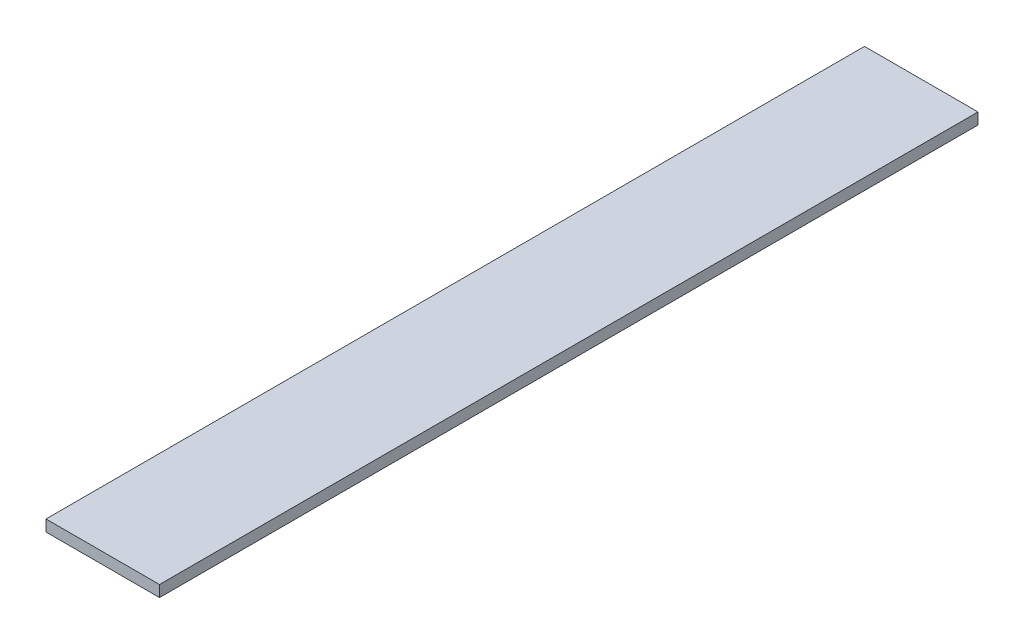
SolidWorks part; units mm, degrees
material "Acrylic (Medium-high impact)"
ref_plane "Front Plane" through (0, 0, 0) normal (0, 0, 1) x (1, 0, 0)
ref_plane "Top Plane" through (0, 0, 0) normal (0, 1, 0) x (1, 0, 0)
ref_plane "Right Plane" through (0, 0, 0) normal (1, 0, 0) x (0, 0, -1)
sketch "Sketch1" plane through (0, 0, 0) normal (0, 0, 1) x (1, 0, 0)
  line L1 (0, 0) -> (47.7, 0)
  line L2 (0, 0) -> (0, 4.7625)
  line L3 (0, 4.7625) -> (47.7, 4.7625)
  line L4 (47.7, 0) -> (47.7, 4.7625)
  dimension "D1" = 47.7
  dimension "D2" = 4.7625
extrude "Boss-Extrude1" add sketch "Sketch1" along normal blind 343.95
sketch "Sketch4" plane through (0, 4.7625, -4.7625) normal (0, -1, 0) x (1, 0, 0)
  line L0 (44.525, 9.525) -> (44.525, -49.6327) construction
  line L2 (23.85, 32.8593) -> (23.85, 4.7625) construction
  line L3 (47.7, 4.7625) -> (0, 4.7625) construction
  line L4 (45.922, 4.7625) -> (43.128, 4.7625)
  line L5 (45.922, 4.7625) -> (45.922, 14.2875)
  line L6 (45.922, 14.2875) -> (43.128, 14.2875)
  line L7 (43.128, 4.7625) -> (43.128, 14.2875)
  line L8 (45.922, 4.7625) -> (43.128, 14.2875) construction
  line L9 (45.922, 14.2875) -> (43.128, 4.7625) construction
  point P2 (23.85, 4.7625)
  point P6 (44.525, 9.525)
  point P12 (44.525, 9.525)
  point P13 (23.85, 32.8593)
  point P14 (44.525, 9.9079)
  dimension "D1" = 20.675
  dimension "D2" = 2.794
  dimension "D3" = 9.525
